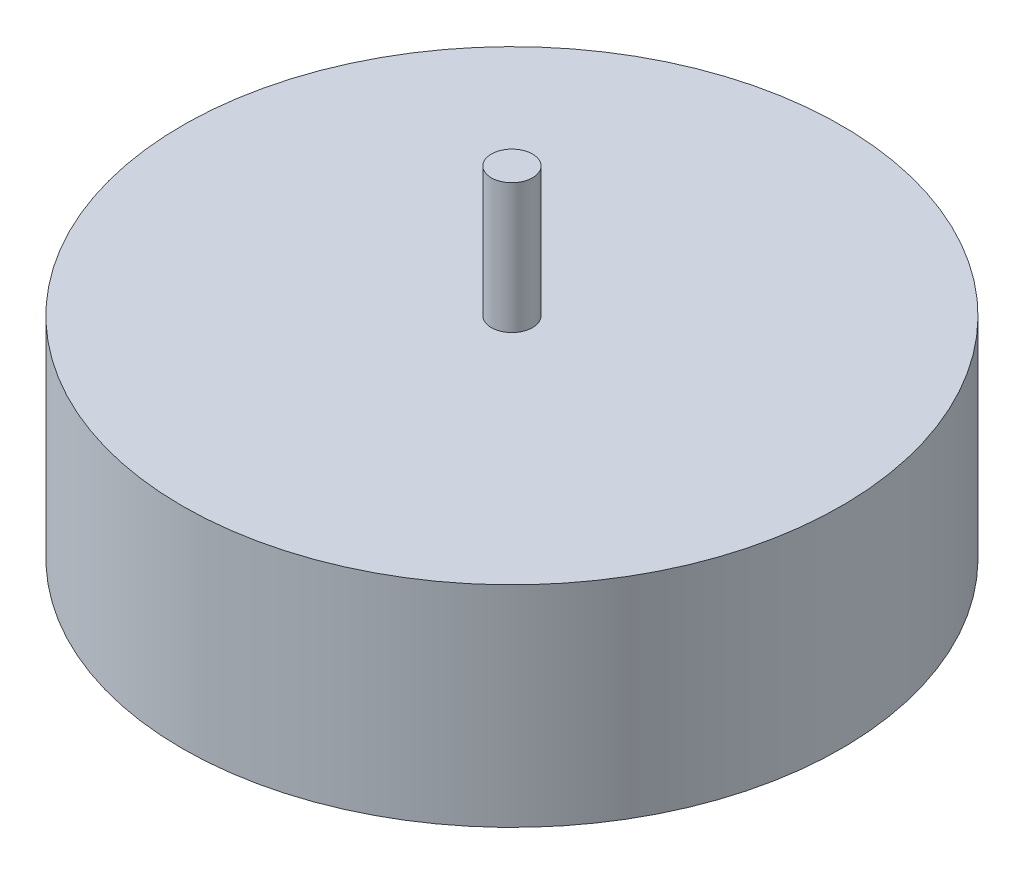
SolidWorks part; units mm, degrees
ref_plane "Front Plane" through (0, 0, 0) normal (0, 0, 1) x (1, 0, 0)
ref_plane "Top Plane" through (0, 0, 0) normal (0, 1, 0) x (1, 0, 0)
ref_plane "Right Plane" through (0, 0, 0) normal (1, 0, 0) x (0, 0, -1)
sketch "Sketch1" plane through (0, 0, 0) normal (0, 1, 0) x (1, 0, 0)
  circle A0 centre (0, 0) radius 127
  dimension "D1" = 254
extrude "Boss-Extrude1" add sketch "Sketch1" along normal blind 80.96
sketch "Sketch2" plane through (0, 80.96, 0) normal (0, 1, 0) x (1, 0, 0)
  circle A0 centre (0, 0) radius 7.9375
  dimension "D1" = 15.875
extrude "Boss-Extrude2" add sketch "Sketch2" along normal blind 50
